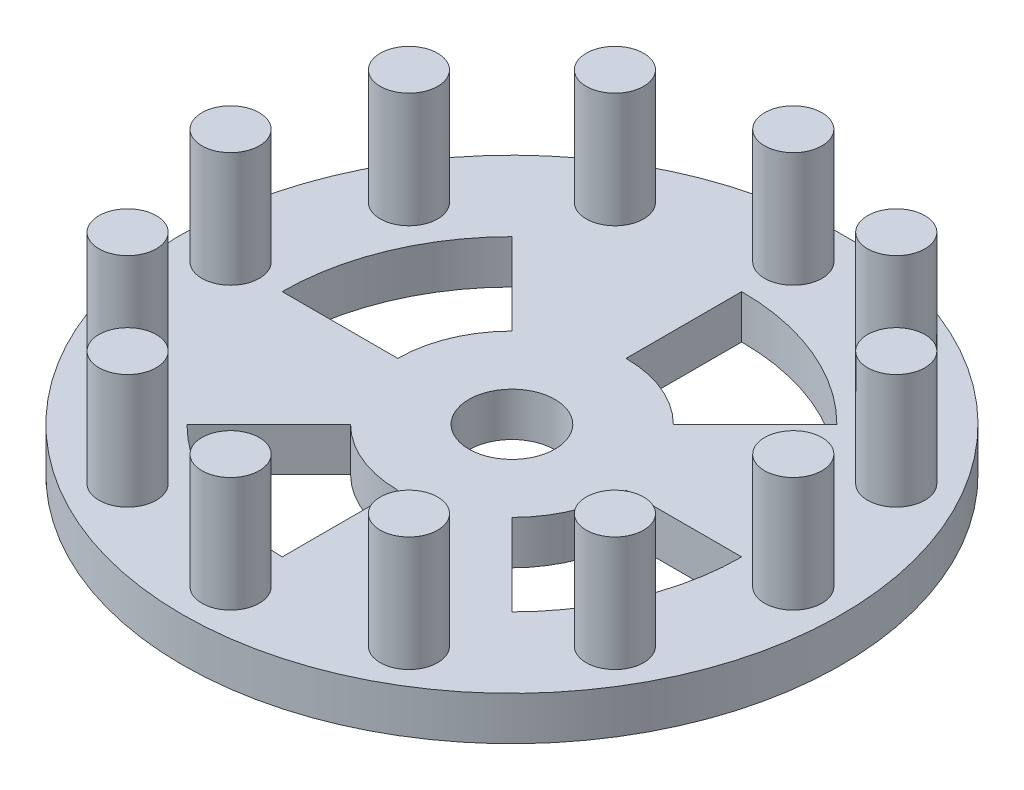
SolidWorks part; units mm, degrees
ref_plane "Front Plane" through (0, 0, 0) normal (0, 0, 1) x (1, 0, 0)
ref_plane "Top Plane" through (0, 0, 0) normal (0, 1, 0) x (1, 0, 0)
ref_plane "Right Plane" through (0, 0, 0) normal (1, 0, 0) x (0, 0, -1)
sketch "Sketch1" plane through (0, 0, 0) normal (0, 1, 0) x (1, 0, 0)
  circle A0 centre (31.8964, 77.0049) radius 36.449
  circle A1 centre (31.8964, 77.0049) radius 4.7625
  dimension "D1" = 72.898
  dimension "D2" = 9.525
extrude "Extrude1" add sketch "Sketch1" along normal blind 4.826
sketch "Sketch2" plane through (0, 4.826, 0) normal (0, 1, 0) x (1, 0, 0)
  line L0 (-9.9521, 77.0049) -> (81.5834, 77.0049) construction
  circle A0 centre (31.8964, 77.0049) radius 31.115 construction
  circle A4 centre (63.0114, 77.0049) radius 3.175
  dimension "D1" = 62.23
  dimension "D2" = 6.35
extrude "Extrude2" add sketch "Sketch2" along normal blind 12.7
pattern_circular "CirPattern1" count 12 over 360 about axis through (31.8964, 0, -77.0049) along (0, 1, 0) of "Extrude2"
sketch "Sketch3" plane through (0, 4.826, 0) normal (0, 1, 0) x (1, 0, 0)
  line L0 (31.8964, 89.6244) -> (31.8964, 102.4167)
  line L1 (40.8198, 85.9283) -> (49.8653, 94.9738)
  arc A0 (49.8653, 94.9738) -> (31.8964, 102.4167) centre (31.8964, 77.0049) ccw
  arc A1 (40.8198, 85.9283) -> (31.8964, 89.6244) centre (31.8964, 77.0049) ccw
extrude "Extrude3" cut sketch "Sketch3" against normal blind 19.05
pattern_circular "CirPattern2" count 4 over 360 about axis through (31.8964, 4.826, -77.0049) along (0, 1, 0) of "Extrude3"
